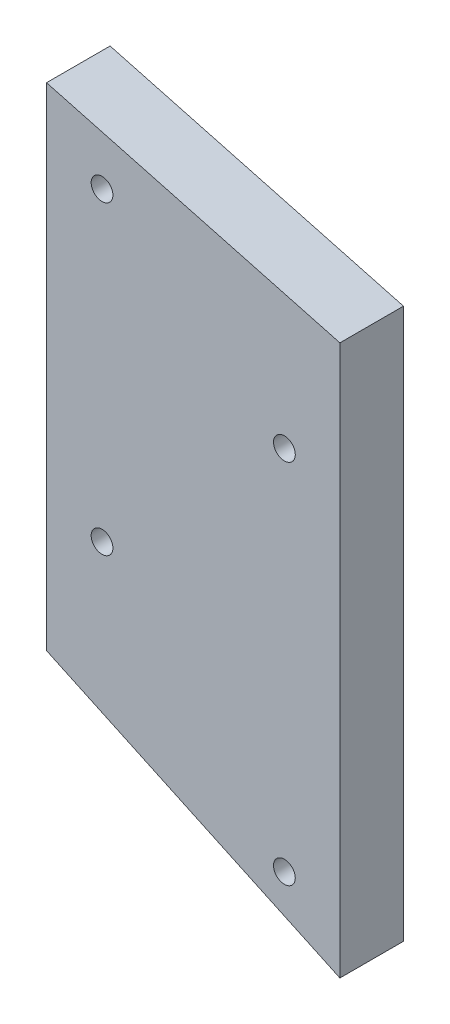
SolidWorks part; units mm, degrees
material "Acrylic (BLUE)"
ref_plane "Front Plane" through (0, 0, 0) normal (0, 0, 1) x (1, 0, 0)
ref_plane "Top Plane" through (0, 0, 0) normal (0, 1, 0) x (1, 0, 0)
ref_plane "Right Plane" through (0, 0, 0) normal (1, 0, 0) x (0, 0, -1)
sketch "Sketch1" plane through (0, 0, 0) normal (0, 0, 1) x (1, 0, 0)
  line L0 (-15.24, 32.6585) -> (15.24, -32.6585) construction
  line L1 (15.24, -32.6585) -> (-15.24, -18.4455)
  line L2 (-15.24, 32.6585) -> (-15.24, -18.4455)
  line L3 (0, 0) -> (-26.8117, 0) construction
  line L4 (15.24, 24.4915) -> (15.24, -32.6585)
  line L5 (-15.24, 32.6585) -> (15.24, 24.4915)
  dimension "D1" = 30.48
  dimension "D2" = 15
  dimension "D3" = 57.15
  dimension "D4" = 25
extrude "Boss-Extrude1" add sketch "Sketch1" along normal blind 6.604
hole_wizard "#4-40 Tapped Hole1" positions "Sketch3" profile "Sketch2" tap size "#4-40" standard "ANSI Inch"
sketch "Sketch3" plane through (0, 0, 6.604) normal (0, 0, 1) x (1, 0, 0)
  line L0 (-9.4742, 25.9842) -> (9.4742, 25.9842) construction
  line L1 (9.4742, 25.9842) -> (9.4742, 12.1158) construction
  line L3 (-9.4742, -5.7658) -> (-9.4742, 25.9842) construction
  line L5 (-9.4742, -5.7658) -> (9.4742, -5.7658) construction
  line L6 (9.4742, -5.7658) -> (9.4742, -25.9842) construction
  line L7 (-9.4742, 25.9842) -> (9.4742, -25.9842) construction
  point P0 (-9.4742, 25.9842)
  point P2 (9.4742, 12.1158)
  point P4 (-9.4742, -5.7658)
  point P6 (9.4742, -25.9842)
  dimension "D1" = 18.9484
  dimension "D2" = 13.8684
  dimension "D3" = 31.75
  dimension "D4" = 38.1
sketch "Sketch2" plane through (-9.4742, 25.9842, 6.604) normal (1, 0, 0) x (0, -1, 0)
  line L0 (0, 0) -> (0, 8.2738)
  line L1 (0, 8.2738) -> (1.1303, 7.5946)
  line L2 (1.1303, 7.5946) -> (1.1303, 0)
  line L5 (1.1303, 0) -> (0, 0)
  line L10 (0, 8.2738) -> (-1.1303, 7.5946) construction
  line L11 (0, -6.35) -> (0, 107.95) construction
  dimension "Tap Drill Dia." = 2.2606
  dimension "Tap Drill Depth" = 7.5946
  dimension "Drill Angle" = 118
other "Move Face1" [suppressed] parameters "D1"=0.127
